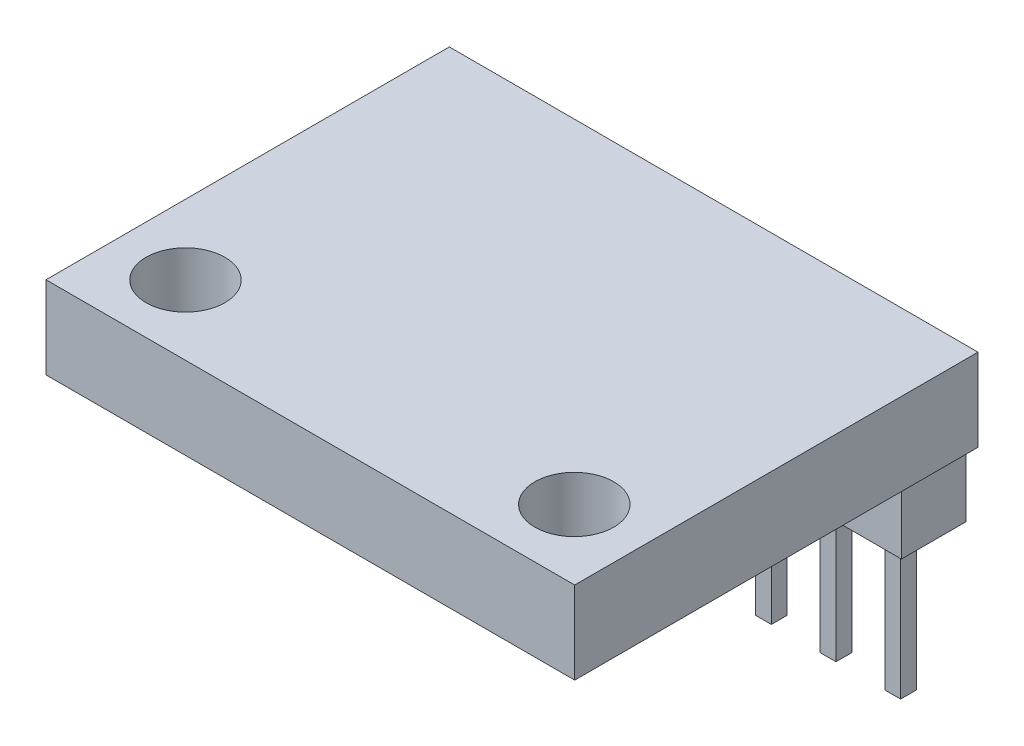
SolidWorks part; units mm, degrees
ref_plane "Front Plane" through (0, 0, 0) normal (0, 0, 1) x (1, 0, 0)
ref_plane "Top Plane" through (0, 0, 0) normal (0, 1, 0) x (1, 0, 0)
ref_plane "Right Plane" through (0, 0, 0) normal (1, 0, 0) x (0, 0, -1)
sketch "Sketch1" plane through (0, 0, 0) normal (0, 1, 0) x (1, 0, 0)
  line L0 (0, -8.7173) -> (0, 8.7173) construction
  line L1 (-1.9939, 1.9939) -> (1.9939, 1.9939) construction
  line L2 (-1.9939, 1.9939) -> (-1.9939, -1.9939) construction
  line L3 (-1.9939, -1.9939) -> (1.9939, -1.9939) construction
  line L4 (1.9939, 1.9939) -> (1.9939, -1.9939) construction
  line L5 (-1.9939, 1.9939) -> (1.9939, -1.9939) construction
  line L6 (-1.9939, -1.9939) -> (1.9939, 1.9939) construction
  line L7 (-10.3886, 8.6487) -> (10.3886, 8.6487)
  line L8 (-10.3886, 8.6487) -> (-10.3886, -7.2009)
  line L9 (-10.3886, -7.2009) -> (10.3886, -7.2009)
  line L10 (10.3886, 8.6487) -> (10.3886, -7.2009)
  line L11 (-10.3886, 8.6487) -> (10.3886, -7.2009) construction
  line L12 (-10.3886, -7.2009) -> (10.3886, 8.6487) construction
  circle A0 centre (7.6403, -4.4679) radius 1.5494
  circle A1 centre (-7.6403, -4.4679) radius 1.5494
  point P0 (0, 0)
  point P6 (0, 0.7239)
  point P15 (9.1897, -4.4679)
  point P16 (7.6403, -6.0173)
  dimension "D8" = 3.0988
  dimension "D1" = 3.9878
  dimension "D2" = 3.9878
  dimension "D3" = 9.1948
  dimension "D4" = 15.8496
  dimension "D5" = 20.7772
  dimension "D6" = 1.1836
  dimension "D7" = 1.1989
extrude "Boss-Extrude2" add sketch "Sketch1" along normal blind 3.2385
sketch "Sketch2" plane through (0, 0, 0) normal (0, 1, 0) x (1, 0, 0)
  line L0 (0, -1.7812) -> (0, 1.7812) construction
  line L1 (-10.2489, 5.7785) -> (10.2489, 5.7785)
  line L2 (-10.2489, 5.7785) -> (-10.2489, 8.3185)
  line L3 (-10.2489, 8.3185) -> (10.2489, 8.3185)
  line L4 (10.2489, 5.7785) -> (10.2489, 8.3185)
  line L5 (-10.2489, 5.7785) -> (10.2489, 8.3185) construction
  line L6 (-10.2489, 8.3185) -> (10.2489, 5.7785) construction
  line L7 (10.3886, 8.6487) -> (-10.3886, 8.6487) construction
  point P0 (0, 7.0485)
  dimension "D1" = 0.3302
  dimension "D2" = 20.4978
  dimension "D3" = 2.54
extrude "Boss-Extrude3" add sketch "Sketch2" against normal blind 2.4384
sketch "Sketch3" plane through (0, -2.4384, 0) normal (0, -1, 0) x (1, 0, 0)
  line L0 (-10.2489, -7.0485) -> (10.2489, -7.0485) construction
  line L1 (-10.2489, -8.3185) -> (-10.2489, -5.7785) construction
  line L2 (10.2489, -5.7785) -> (10.2489, -8.3185) construction
  line L3 (-6.604, -6.7374) -> (-6.604, -7.3597)
  line L4 (-9.144, -6.7374) -> (-8.5217, -6.7374)
  line L5 (-9.144, -6.7374) -> (-9.144, -7.3597)
  line L6 (-9.144, -7.3597) -> (-8.5217, -7.3597)
  line L7 (-8.5217, -6.7374) -> (-8.5217, -7.3597)
  line L8 (-9.144, -6.7374) -> (-8.5217, -7.3597) construction
  line L9 (-9.144, -7.3597) -> (-8.5217, -6.7374) construction
  line L10 (-6.604, -6.7374) -> (-5.9817, -6.7374)
  line L11 (-5.9817, -6.7374) -> (-5.9817, -7.3597)
  line L12 (-6.604, -7.3597) -> (-5.9817, -7.3597)
  line L13 (-4.064, -6.7374) -> (-4.064, -7.3597)
  line L14 (-4.064, -6.7374) -> (-3.4417, -6.7374)
  line L15 (-3.4417, -6.7374) -> (-3.4417, -7.3597)
  line L16 (-4.064, -7.3597) -> (-3.4417, -7.3597)
  line L17 (-1.524, -6.7374) -> (-1.524, -7.3597)
  line L18 (-1.524, -6.7374) -> (-0.9017, -6.7374)
  line L19 (-0.9017, -6.7374) -> (-0.9017, -7.3597)
  line L20 (-1.524, -7.3597) -> (-0.9017, -7.3597)
  line L21 (1.016, -6.7374) -> (1.016, -7.3597)
  line L22 (1.016, -6.7374) -> (1.6383, -6.7374)
  line L23 (1.6383, -6.7374) -> (1.6383, -7.3597)
  line L24 (1.016, -7.3597) -> (1.6383, -7.3597)
  line L25 (3.556, -6.7374) -> (3.556, -7.3597)
  line L26 (3.556, -6.7374) -> (4.1783, -6.7374)
  line L27 (4.1783, -6.7374) -> (4.1783, -7.3597)
  line L28 (3.556, -7.3597) -> (4.1783, -7.3597)
  line L29 (6.096, -6.7374) -> (6.096, -7.3597)
  line L30 (6.096, -6.7374) -> (6.7183, -6.7374)
  line L31 (6.7183, -6.7374) -> (6.7183, -7.3597)
  line L32 (6.096, -7.3597) -> (6.7183, -7.3597)
  line L33 (8.636, -6.7374) -> (8.636, -7.3597)
  line L34 (8.636, -6.7374) -> (9.2583, -6.7374)
  line L35 (9.2583, -6.7374) -> (9.2583, -7.3597)
  line L36 (8.636, -7.3597) -> (9.2583, -7.3597)
  point P6 (-8.8329, -7.0485)
  dimension "D1" = 1.1049
  dimension "D2" = 0.6223
  dimension "D4" = 2.54
  dimension "D3" = 8
extrude "Boss-Extrude4" add sketch "Sketch3" along normal blind 5.7404
